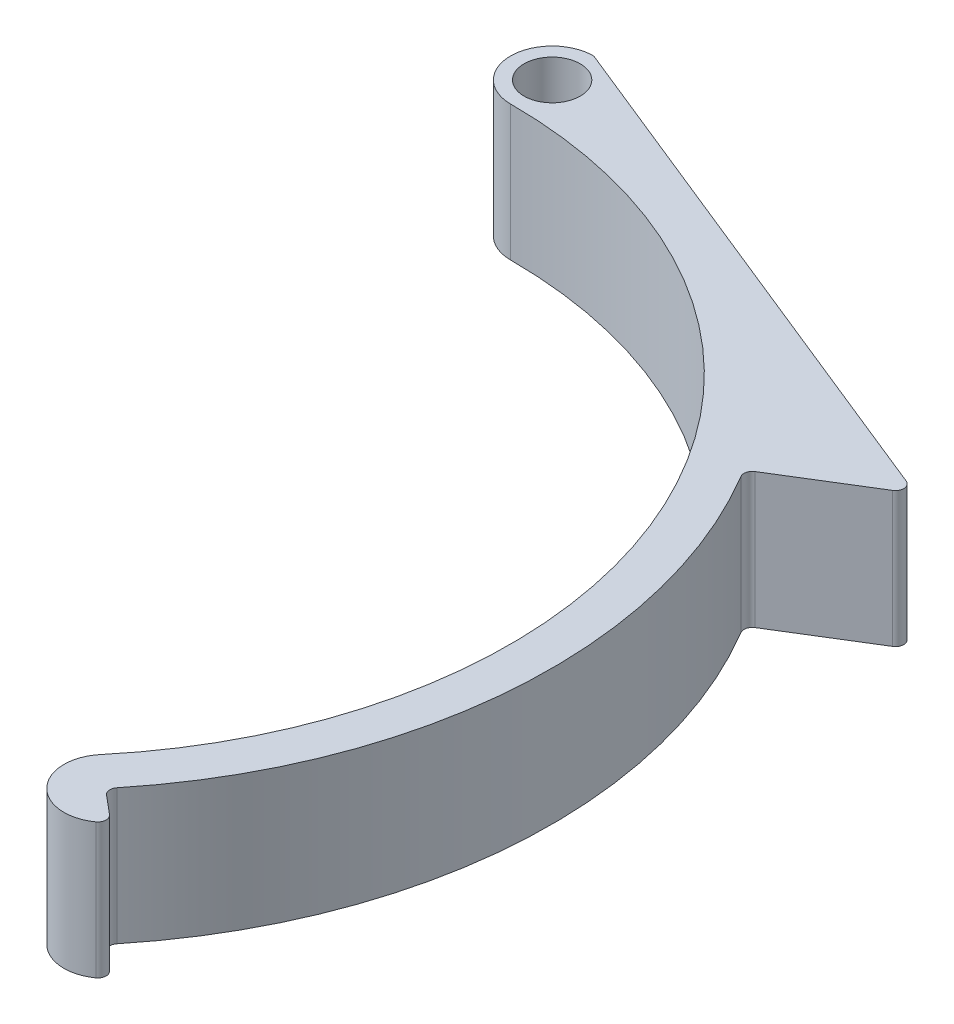
SolidWorks part; units mm, degrees
ref_plane "Front Plane" through (0, 0, 0) normal (0, 0, 1) x (1, 0, 0)
ref_plane "Top Plane" through (0, 0, 0) normal (0, 1, 0) x (1, 0, 0)
ref_plane "Right Plane" through (0, 0, 0) normal (1, 0, 0) x (0, 0, -1)
sketch "Sketch1" plane through (0, 0, 0) normal (0, 1, 0) x (1, 0, 0)
  line L0 (0, 0) -> (34.472, -28.9254) construction
  line L1 (0, 0) -> (0, -45) construction
  line L2 (0, 0) -> (63.5762, -53.3468) construction
  line L3 (0, 53) -> (51.921, 32.0189)
  line L4 (51.921, 32.0189) -> (41.707, 25.7201)
  line L5 (0, 53) -> (0, 49)
  line L6 (37.5362, -31.4966) -> (40.6004, -34.0677)
  line L7 (0, 49) -> (0, 53)
  circle A0 centre (0, 0) radius 45 construction
  arc A1 (0, 45) -> (34.472, -28.9254) centre (0, 0) cw
  arc A2 (0, 45) -> (0, 53) centre (0, 49) cw
  arc A3 (34.472, -28.9254) -> (40.6004, -34.0677) centre (37.5362, -31.4966) ccw
  arc A4 (37.5362, -31.4966) -> (0, 49) centre (0, 0) ccw
  circle A5 centre (0, 49) radius 2.7
  arc A6 (41.707, 25.7201) -> (0, 49) centre (0, 0) ccw
  dimension "D1" = 90
  dimension "D5" = 56
  dimension "D6" = 5.4
  dimension "D2" = 50
  dimension "D3" = 8
  dimension "D4" = 4
  dimension "D7" = 12
extrude "Boss-Extrude1" add sketch "Sketch1" along normal blind 13 contours A5 L5 A2 A1 A3 L6 A4 | A5 A4 L4 L3 L5
fillet "Fillet1" radius 0.8 5 edges at (0, 6.5, -53) (37.5362, 6.5, 31.4966) (40.6004, 6.5, 34.0677) (51.921, 6.5, -32.0189) (41.707, 6.5, -25.7201)
